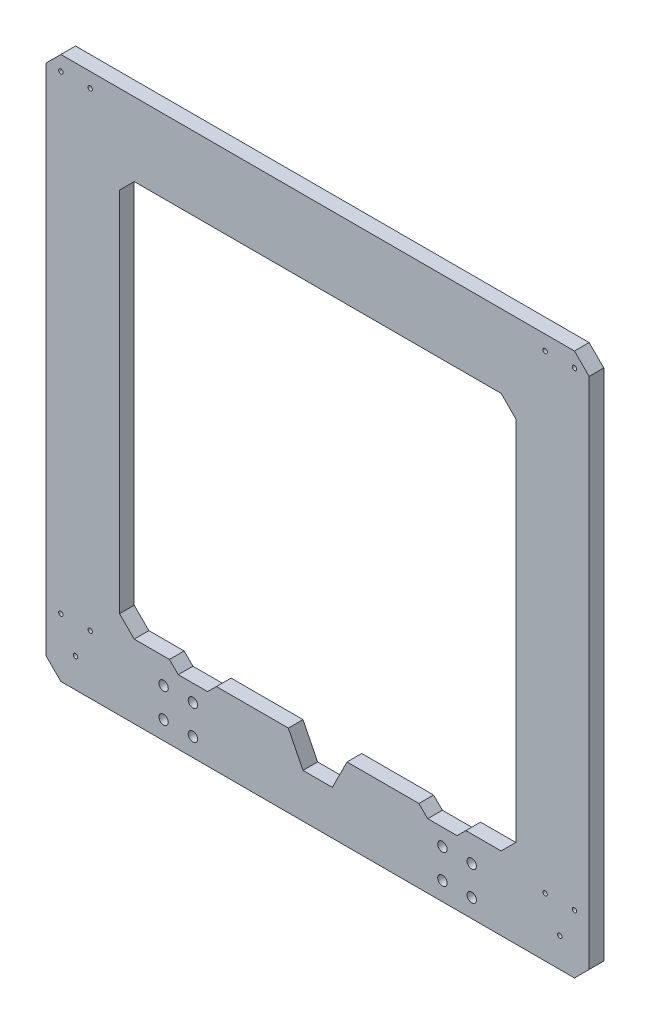
SolidWorks part; units mm, degrees
material "Pine"
ref_plane "Front Plane" through (0, 0, 0) normal (0, 0, 1) x (1, 0, 0)
ref_plane "Top Plane" through (0, 0, 0) normal (0, 1, 0) x (1, 0, 0)
ref_plane "Right Plane" through (0, 0, 0) normal (1, 0, 0) x (0, 0, -1)
sketch "Sketch1" plane through (0, 0, 0) normal (0, 0, 1) x (1, 0, 0)
  line L0 (0, -185) -> (0, -135) construction
  line L1 (-185, -185) -> (185, -185)
  line L2 (-185, -185) -> (-185, 185)
  line L3 (-185, 185) -> (185, 185)
  line L4 (185, -185) -> (185, 185)
  line L5 (-185, -185) -> (185, 185) construction
  line L6 (-185, 185) -> (185, -185) construction
  line L11 (-135, 135) -> (135, 135)
  line L12 (-135, 135) -> (-135, -135)
  line L13 (-135, -135) -> (-20, -135)
  line L14 (135, 135) -> (135, -135)
  line L15 (-135, 135) -> (135, -135) construction
  line L16 (-135, -135) -> (135, 135) construction
  line L18 (75, -142.5) -> (95, -142.5) construction
  line L19 (75, -142.5) -> (75, -182.5) construction
  line L20 (75, -182.5) -> (95, -182.5) construction
  line L21 (95, -142.5) -> (95, -182.5) construction
  line L26 (85, -142.5) -> (85, -182.5) construction
  line L27 (-115, -162.5) -> (-95, -162.5) construction
  line L28 (95, -162.5) -> (75, -162.5) construction
  line L29 (-105, -142.5) -> (-105, -182.5) construction
  line L30 (95, -142.5) -> (115, -142.5) construction
  line L31 (95, -142.5) -> (95, -182.5) construction
  line L32 (95, -182.5) -> (115, -182.5) construction
  line L33 (115, -142.5) -> (115, -182.5) construction
  line L34 (105, -142.5) -> (105, -182.5) construction
  line L35 (115, -162.5) -> (95, -162.5) construction
  line L36 (-115, -142.5) -> (-115, -182.5) construction
  line L37 (-95, -182.5) -> (-115, -182.5) construction
  line L38 (-95, -142.5) -> (-95, -182.5) construction
  line L39 (-95, -142.5) -> (-115, -142.5) construction
  line L40 (-95, -162.5) -> (-75, -162.5) construction
  line L41 (-85, -142.5) -> (-85, -182.5) construction
  line L42 (-95, -142.5) -> (-95, -182.5) construction
  line L43 (-75, -182.5) -> (-95, -182.5) construction
  line L44 (-75, -142.5) -> (-75, -182.5) construction
  line L45 (-75, -142.5) -> (-95, -142.5) construction
  line L46 (-185, -185) -> (-185, 185)
  line L47 (185, -185) -> (185, 185)
  line L48 (20, -135) -> (10, -155)
  line L49 (10, -155) -> (-10, -155)
  line L50 (-10, -155) -> (-20, -135)
  line L51 (20, -135) -> (135, -135)
  circle A2 centre (85, -152.5) radius 3.2
  circle A4 centre (85, -172.5) radius 3.2
  circle A6 centre (105, -152.5) radius 3.2
  circle A7 centre (105, -172.5) radius 3.2
  circle A8 centre (-105, -172.5) radius 3.2
  circle A9 centre (-105, -152.5) radius 3.2
  circle A10 centre (-85, -172.5) radius 3.2
  circle A11 centre (-85, -152.5) radius 3.2
  circle A12 centre (155, -145) radius 1.5
  circle A13 centre (175, -145) radius 1.5
  circle A14 centre (165, -165) radius 1.5
  circle A15 centre (-155, -145) radius 1.5
  circle A16 centre (-175, -145) radius 1.5
  circle A17 centre (-165, -165) radius 1.5
  circle A18 centre (155, 175) radius 1.5
  circle A19 centre (175, 175) radius 1.5
  circle A20 centre (-155, 175) radius 1.5
  circle A21 centre (-175, 175) radius 1.5
  point P0 (0, 0)
  point P5 (0, 0)
  dimension "D6" = 2.5
  dimension "D3" = 20
  dimension "D5" = 20
  dimension "D10" = 6.4
  dimension "D11" = 6.4
  dimension "D12" = 3
  dimension "D18" = 20
  dimension "D21" = 3
  dimension "D1" = 370
  dimension "D2" = 50
  dimension "D4" = 40
  dimension "D7" = 170
  dimension "D8" = 40
  dimension "D9" = 20
  dimension "D13" = 20
  dimension "D14" = 10
  dimension "D15" = 20
  dimension "D16" = 10
  dimension "D17" = 20
  dimension "D19" = 10
  dimension "D20" = 10
  dimension "D22" = 20
  dimension "D23" = 40
  dimension "D24" = 20
extrude "Boss-Extrude1" add sketch "Sketch1" along normal blind 10 contours L1 L4 L3 L2 A10 A8 A7 A6 A4 A2 L11 L14 L13 L12 A9 A11
chamfer "Chamfer1" distance 10 angle 45 8 edges at (135, 135, 5) (-135, 135, 5) (-135, -135, 5) (185, -185, 5) (-185, -185, 5) (-185, 185, 5) (185, 185, 5) (135, -135, 5)
sketch "Sketch2" plane through (0, 0, 10) normal (0, 0, 1) x (1, 0, 0)
  line L0 (-101, -135) -> (-95, -141)
  line L1 (-125, -135) -> (-20, -135) construction
  line L3 (-75, -141) -> (-69, -135)
  line L4 (-95, -141) -> (-75, -141)
  line L5 (-101, -135) -> (-69, -135)
  line L6 (-85, -141) -> (-85, -135) construction
  line L11 (0, -185) -> (0, -135) construction
  line L12 (-175, -185) -> (175, -185) construction
  line L13 (75, -141) -> (69, -135)
  line L14 (95, -141) -> (75, -141)
  line L15 (101, -135) -> (95, -141)
  line L16 (101, -135) -> (69, -135)
  point P15 (-85, -141)
  dimension "D1" = 6
  dimension "D2" = 32
  dimension "D3" = 20
  dimension "D4" = 85
extrude "Cut-Extrude1" cut sketch "Sketch2" against normal blind 10
